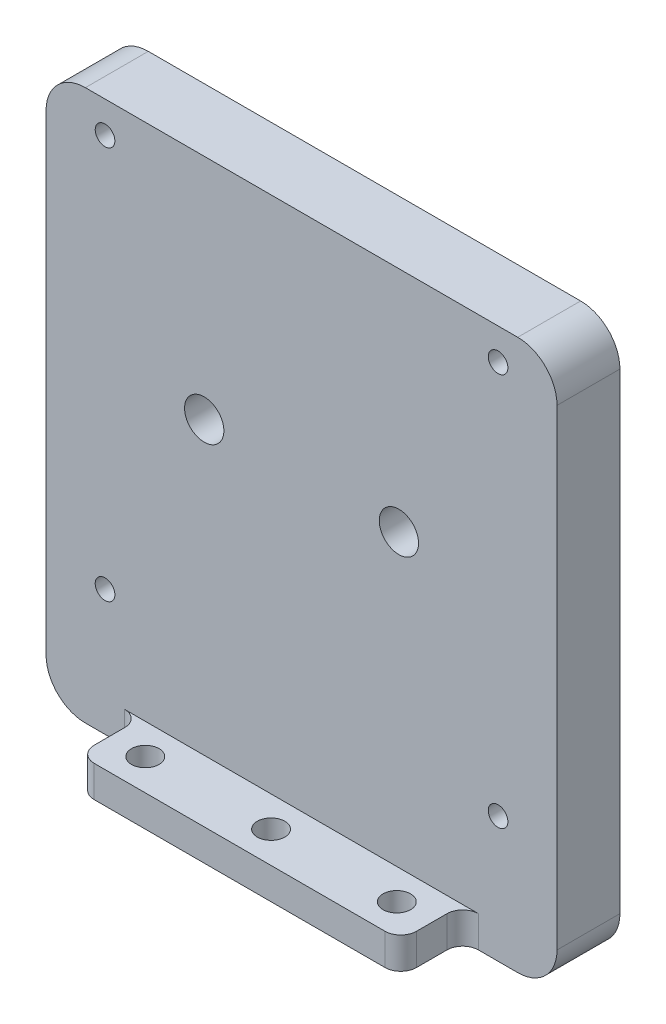
SolidWorks part; units mm, degrees
ref_plane "Front Plane" through (0, 0, 0) normal (0, 0, 1) x (1, 0, 0)
ref_plane "Top Plane" through (0, 0, 0) normal (0, 1, 0) x (1, 0, 0)
ref_plane "Right Plane" through (0, 0, 0) normal (1, 0, 0) x (0, 0, -1)
sketch "Sketch1" plane through (0, 0, 0) normal (0, 0, 1) x (1, 0, 0)
  line L0 (0, 4) -> (0, 0) construction
  line L1 (-32.5, 35) -> (32.5, 35)
  line L2 (-32.5, 35) -> (-32.5, -35)
  line L3 (-32.5, -35) -> (32.5, -35)
  line L4 (32.5, 35) -> (32.5, -35)
  line L5 (-32.5, 35) -> (32.5, -35) construction
  line L6 (-32.5, -35) -> (32.5, 35) construction
  line L7 (25, -21) -> (-25, -21) construction
  line L8 (25, -21) -> (25, 29) construction
  line L9 (25, 29) -> (-25, 29) construction
  line L10 (-25, -21) -> (-25, 29) construction
  line L11 (25, -21) -> (-25, 29) construction
  line L12 (25, 29) -> (-25, -21) construction
  point P0 (0, 0)
  point P6 (0, 4)
  dimension "D1" = 70
  dimension "D2" = 65
  dimension "D4" = 50
  dimension "D5" = 6
extrude "Boss-Extrude1" add sketch "Sketch1" along normal blind 8
fillet "Fillet1" radius 5 4 edges at (32.5, -35, 4) (-32.5, -35, 4) (32.5, 35, 4) (-32.5, 35, 4)
sketch "Sketch2" plane through (0, 0, 8) normal (0, 0, 1) x (1, 0, 0)
  line L0 (-27.5, -35) -> (27.5, -35) construction
  line L1 (-20.5, -35) -> (20.5, -35)
  line L2 (-20.5, -35) -> (-20.5, -31)
  line L3 (-20.5, -31) -> (20.5, -31)
  line L4 (20.5, -35) -> (20.5, -31)
  line L5 (0, 0) -> (0, -31) construction
  dimension "D1" = 41
  dimension "D2" = 4
extrude "Boss-Extrude2" add sketch "Sketch2" along normal blind 7.8799
fillet "Fillet2" radius 2 4 edges at (20.5, -33, 8) (20.5, -33, 15.8799) (-20.5, -33, 15.8799) (-20.5, -33, 8)
sketch "草图1" plane through (0, -35, 0) normal (0, -1, 0) x (1, 0, 0)
  line L0 (-16, 11.8799) -> (0, 11.8799) construction
  line L1 (0, 11.8799) -> (16, 11.8799) construction
  line L2 (-18.5, 15.8799) -> (18.5, 15.8799) construction
  circle A0 centre (-16, 11.8799) radius 1.75
  circle A1 centre (0, 11.8799) radius 1.75
  circle A2 centre (16, 11.8799) radius 1.75
  dimension "D2" = 3.5
  dimension "D1" = 16
  dimension "D3" = 4
extrude "切除-拉伸1" cut sketch "草图1" against normal through all
sketch "草图2" plane through (0, 0, 0) normal (0, 0, -1) x (-1, 0, 0)
  line L0 (-25, 31) -> (25, -19) construction
  line L1 (-25, 31) -> (25, 31) construction
  line L2 (-25, 31) -> (-25, -19) construction
  line L3 (-25, -19) -> (25, -19) construction
  line L4 (25, 31) -> (25, -19) construction
  line L5 (-27.5, 35) -> (27.5, 35) construction
  point P4 (0, 6)
  point P8 (0, 35)
  dimension "D1" = 50
  dimension "D2" = 50
  dimension "D3" = 4
hole_wizard "M3 螺纹孔1" positions "3D草图1" profile "草图3" tap size "M3" standard "ISO"
sketch3d "3D草图1"
  point P0 (25, -19, 0)
  point P3 (25, 31, 0)
  point P6 (-25, 31, 0)
  point P9 (-25, -19, 0)
sketch "草图3" plane through (25, -19, 0) normal (1, 0, 0) x (0, 1, 0)
  line L0 (0, 0) -> (0, 10.7511)
  line L1 (0, 10.7511) -> (1.25, 10)
  line L2 (1.25, 10) -> (1.25, 0)
  line L5 (1.25, 0) -> (0, 0)
  line L10 (0, 10.7511) -> (-1.25, 10) construction
  line L11 (0, -6.35) -> (0, 107.95) construction
  dimension "螺纹孔钻头直径" = 2.5
  dimension "螺纹孔钻头深度" = 10
  dimension "导头角度" = 118
cosmetic thread "孔螺蚊线1" parameters "D1"=6, "D2"=3
cosmetic thread "孔螺蚊线2" parameters "D1"=6, "D2"=3
cosmetic thread "孔螺蚊线3" parameters "D1"=6, "D2"=3
cosmetic thread "孔螺蚊线4" parameters "D1"=6, "D2"=3
ref_plane "基准面1" through (0, 0, -30.31) normal (0, 0, -1) x (-1, 0, 0)
sketch "草图11" plane through (0, 0, -30.31) normal (0, 0, -1) x (-1, 0, 0)
  line L0 (-32.5, 34.15) -> (-32.5, 36.65) construction
  line L1 (32.5, -35) -> (-32.5, -35)
  line L2 (32.5, -35) -> (32.5, 35.4)
  line L3 (32.5, 35.4) -> (-32.5, 35.4)
  line L4 (-32.5, -35) -> (-32.5, 35.4)
extrude "凸台-拉伸1" add sketch "草图11" against normal blind 2.9 separate body
fillet "圆角2" radius 5 1 edges at (-32.5, 35.4, -28.86)
fillet "圆角3" radius 5 1 edges at (-32.5, -35, -28.86)
fillet "圆角4" radius 5 1 edges at (32.5, -35, -28.86)
fillet "圆角5" radius 5 1 edges at (32.5, 35.4, -28.86)
sketch "草图15" plane through (0, 0, -30.31) normal (0, 0, -1) x (-1, 0, 0)
  circle A0 centre (-25, -19) radius 1.7
  circle A1 centre (-25, 31) radius 1.7
  circle A2 centre (25, -19) radius 1.7
  circle A3 centre (25, 31) radius 1.7
hole_wizard "M3 螺纹孔2" positions "草图23" profile "草图24" tap size "M3" standard "ISO" end condition up to next
sketch "草图23" plane through (0, 0, -30.31) normal (0, 0, -1) x (-1, 0, 0)
  point P0 (-25, 31)
  point P3 (25, 31)
  point P6 (-25, -19)
  point P9 (25, -19)
cosmetic thread "孔螺蚊线5" parameters "D2"=3
cosmetic thread "孔螺蚊线6" parameters "D2"=3
cosmetic thread "孔螺蚊线7" parameters "D2"=3
cosmetic thread "孔螺蚊线8" parameters "D2"=3
sketch "草图24" plane through (25, 31, -30.31) normal (1, 0, 0) x (0, 1, 0)
  line L0 (0, 0) -> (0, 2.901)
  line L1 (0, 2.901) -> (1.25, 2.901)
  line L2 (1.25, 2.901) -> (1.25, 0)
  line L5 (1.25, 0) -> (0, 0)
  line L11 (0, -6.35) -> (0, 107.95) construction
  dimension "通孔螺纹孔钻头直径" = 2.5
  dimension "通孔螺纹孔钻头深度" = 2.901
hole_wizard "M4 六角凹头螺钉的柱形沉头孔2" positions "草图26" profile "草图27" counterbore size "M4" standard "ISO" end condition up to next
sketch "草图26" plane through (0, 0, -30.31) normal (0, 0, -1) x (-1, 0, 0)
  point P0 (-9.4177, -9.82)
  point P3 (7.7273, -9.82)
  point P6 (7.7272, 19.876)
  point P9 (-9.4178, 19.876)
sketch "草图27" plane through (9.4177, -9.82, -30.31) normal (1, 0, 0) x (0, 1, 0)
  line L0 (0, 0) -> (0, 38.31)
  line L1 (0, 38.31) -> (2.25, 38.31)
  line L3 (2.25, 38.31) -> (2.25, 1.5)
  line L4 (2.25, 1.5) -> (4, 1.5)
  line L5 (4, 1.5) -> (4, 0)
  line L7 (4, 0) -> (0, 0)
  line L11 (0, -6.35) -> (0, 107.95) construction
  dimension "通孔孔直径" = 4.5
  dimension "通孔孔深度" = 38.31
  dimension "柱形沉头孔直径" = 8
  dimension "柱形沉头孔深度" = 1.5
sketch "草图28" plane through (32.5, 0, 0) normal (1, 0, 0) x (0, 0, -1)
  line L1 (21.2827, 40.5552) -> (37.6286, 40.5552)
  line L2 (21.2827, 40.5552) -> (21.2827, -44.2702)
  line L3 (21.2827, -44.2702) -> (37.6286, -44.2702)
  line L4 (37.6286, 40.5552) -> (37.6286, -44.2702)
extrude "切除-拉伸4" cut sketch "草图28" against normal through all
sketch "草图29" plane through (0, 0, 0) normal (0, 0, -1) x (-1, 0, 0)
  line L0 (-12.3825, 6) -> (12.3825, 6) construction
  line L1 (25, 31) -> (25, -19) construction
  line L2 (-25, -19) -> (25, -19) construction
  point P2 (0, 6)
  point P5 (25, 6)
  point P9 (0, -19)
  dimension "D1" = 24.765
hole_wizard "M6 螺纹孔1" positions "3D草图2" profile "草图30" tap size "M6" standard "ISO" end condition through all
sketch3d "3D草图2"
  point P0 (12.3825, 6, 0)
  point P3 (-12.3825, 6, 0)
cosmetic thread "孔螺蚊线9" parameters "D2"=6
cosmetic thread "孔螺蚊线10" parameters "D2"=6
sketch "草图30" plane through (12.3825, 6, 0) normal (1, 0, 0) x (0, 1, 0)
  line L0 (0, 0) -> (0, 15.8799)
  line L1 (0, 15.8799) -> (2.5, 15.8799)
  line L2 (2.5, 15.8799) -> (2.5, 0)
  line L5 (2.5, 0) -> (0, 0)
  line L11 (0, -6.35) -> (0, 107.95) construction
  dimension "通孔螺纹孔钻头直径" = 5
  dimension "通孔螺纹孔钻头深度" = 15.8799
